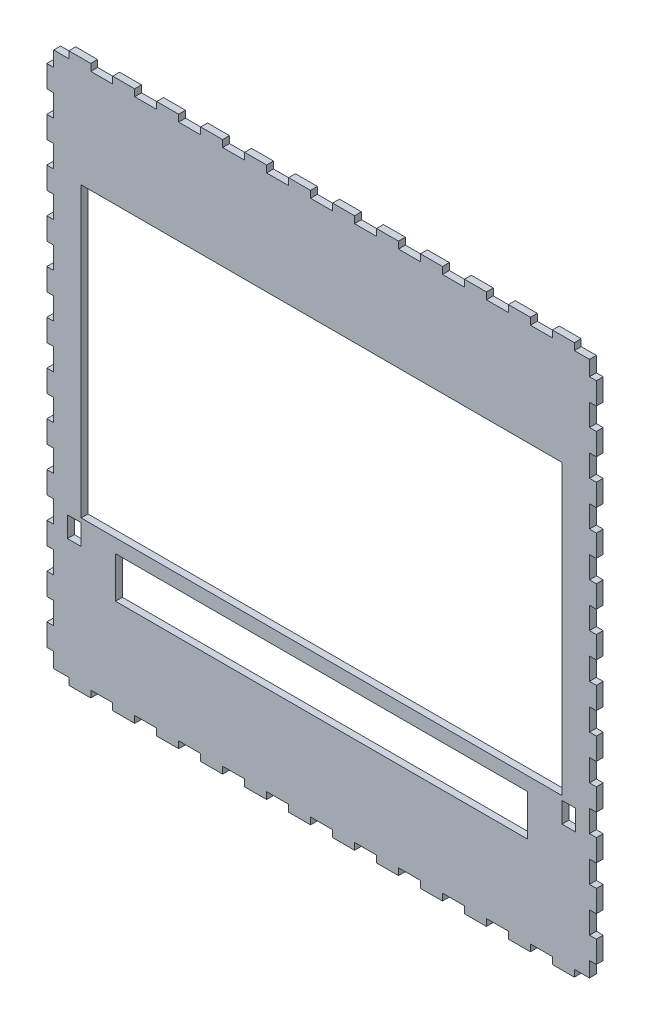
SolidWorks part; units mm, degrees
ref_plane "Plan de face" through (0, 0, 0) normal (0, 0, 1) x (1, 0, 0)
ref_plane "Plan de dessus" through (0, 0, 0) normal (0, 1, 0) x (1, 0, 0)
ref_plane "Plan de droite" through (0, 0, 0) normal (1, 0, 0) x (0, 0, -1)
sketch "Esquisse1" plane through (0, 0, 0) normal (0, 0, 1) x (1, 0, 0)
  line L1 (0, 0) -> (400, 0)
  line L2 (0, 0) -> (0, -400)
  line L3 (0, -400) -> (400, -400)
  line L4 (400, 0) -> (400, -400)
  line L5 (25, -80) -> (375, -80)
  line L6 (25, -80) -> (25, -290)
  line L7 (25, -290) -> (375, -290)
  line L8 (375, -80) -> (375, -290)
  line L9 (50, -300) -> (350, -300)
  line L10 (50, -300) -> (50, -330)
  line L11 (50, -330) -> (350, -330)
  line L12 (350, -300) -> (350, -330)
  dimension "D2" = 400
  dimension "D1" = 400
  dimension "D3" = 80
  dimension "D4" = 25
  dimension "D6" = 110
  dimension "D7" = 30
  dimension "D8" = 10
  dimension "D9" = 300
  dimension "D10" = 25
  dimension "D5" = 25
extrude "Boss.-Extru.1" add sketch "Esquisse1" along normal blind 5
sketch "Esquisse2" plane through (0, 0, 5) normal (0, 0, 1) x (1, 0, 0)
  line L0 (0, -395) -> (0, -400)
  line L3 (0, -395) -> (16, -395)
  line L4 (16, -400) -> (16, -395)
  line L5 (0, -400) -> (16, -400)
  line L8 (0, -400) -> (400, -400) construction
  dimension "D1" = 5
  dimension "D2" = 16
  dimension "D3" = 400
extrude "Enlèv. mat.-Extru.1" cut sketch "Esquisse2" against normal blind 5
pattern_linear "Répétition linéaire1" count 13 spacing 32 along (1, 0, 0) of "Enlèv. mat.-Extru.1"
ref_plane "Plan1" through (0, -200, 0) normal (0, -1, 0) x (-1, 0, 0)
mirror "Symétrie1" about plane through (0, -200, 0) normal (0, -1, 0) of "Répétition linéaire1", "Enlèv. mat.-Extru.1"
ref_plane "Plan2" through (200, 0, 0) normal (-1, 0, 0) x (0, 0, 1)
sketch "Esquisse3" plane through (0, 0, 5) normal (0, 0, 1) x (1, 0, 0)
  line L0 (19.4538, -400) -> (19.4538, 0) construction
  line L1 (0, -400) -> (5, -400)
  line L2 (0, -400) -> (0, -384)
  line L3 (0, -384) -> (5, -384)
  line L4 (5, -400) -> (5, -384)
  line L5 (16, -400) -> (32, -400) construction
  line L6 (32, 0) -> (16, 0) construction
  line L7 (0, -5) -> (0, -395) construction
  dimension "D1" = 5
  dimension "D2" = 400
  dimension "D3" = 16
extrude "Enlèv. mat.-Extru.2" cut sketch "Esquisse3" against normal blind 10
pattern_linear "Répétition linéaire2" count 13 spacing 32 along (0, 1, 0) of "Enlèv. mat.-Extru.2"
mirror "Symétrie2" about plane through (200, 0, 0) normal (-1, 0, 0) of "Répétition linéaire2", "Enlèv. mat.-Extru.2"
sketch "Esquisse4" plane through (0, 0, 5) normal (0, 0, 1) x (1, 0, 0)
  line L0 (395, -304) -> (395, -288) construction
  line L1 (385, -293) -> (375, -293)
  line L2 (385, -293) -> (385, -308)
  line L3 (385, -308) -> (375, -308)
  line L4 (375, -293) -> (375, -308)
  line L5 (25, -290) -> (375, -290) construction
  dimension "D1" = 10
  dimension "D2" = 10
  dimension "D3" = 15
  dimension "D4" = 3
extrude "Enlèv. mat.-Extru.3" cut sketch "Esquisse4" against normal blind 5
mirror "Symétrie3" about plane through (200, 0, 0) normal (-1, 0, 0) of "Enlèv. mat.-Extru.3"
equation "\"D2@Esquisse2\"=\"D3@Esquisse2\"/25"
equation "\"D3@Esquisse3\"=\"D2@Esquisse3\"/25"
equation "\"D10@Esquisse1\"=(\"D1@Esquisse1\"-2*\"D5@Esquisse1\"-\"D9@Esquisse1\")/2"
equation "\"D5@Esquisse1\"=\"D4@Esquisse1\""
